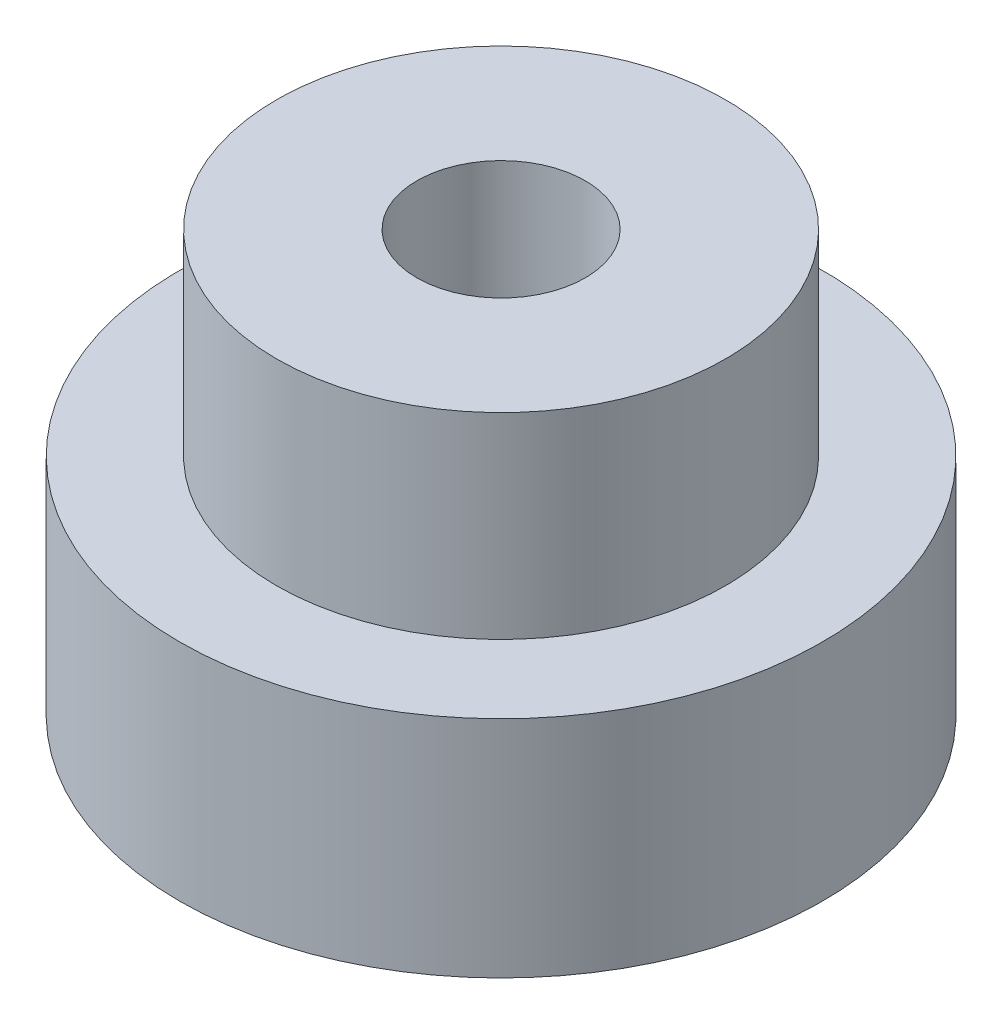
SolidWorks part; units mm, degrees
ref_plane "Front Plane" through (0, 0, 0) normal (0, 0, 1) x (1, 0, 0)
ref_plane "Top Plane" through (0, 0, 0) normal (0, 1, 0) x (1, 0, 0)
ref_plane "Right Plane" through (0, 0, 0) normal (1, 0, 0) x (0, 0, -1)
sketch "Sketch1" plane through (0, 0, 0) normal (0, 1, 0) x (1, 0, 0)
  circle A0 centre (0, 0) radius 11.46
  circle A1 centre (0, 0) radius 8
  circle A2 centre (0, 0) radius 3
  dimension "D1" = 22.92
  dimension "D2" = 16
  dimension "D3" = 6
extrude "Boss-Extrude1" add sketch "Sketch1" along normal blind 8 contours A0 A1
sketch "Sketch2" plane through (0, 8, 0) normal (0, 1, 0) x (1, 0, 0)
  circle A1 centre (0, 0) radius 8
  circle A2 centre (0, 0) radius 3
  dimension "D1" = 6
extrude "Boss-Extrude2" add sketch "Sketch2" along normal blind 7 separate body contours A2 | A1
